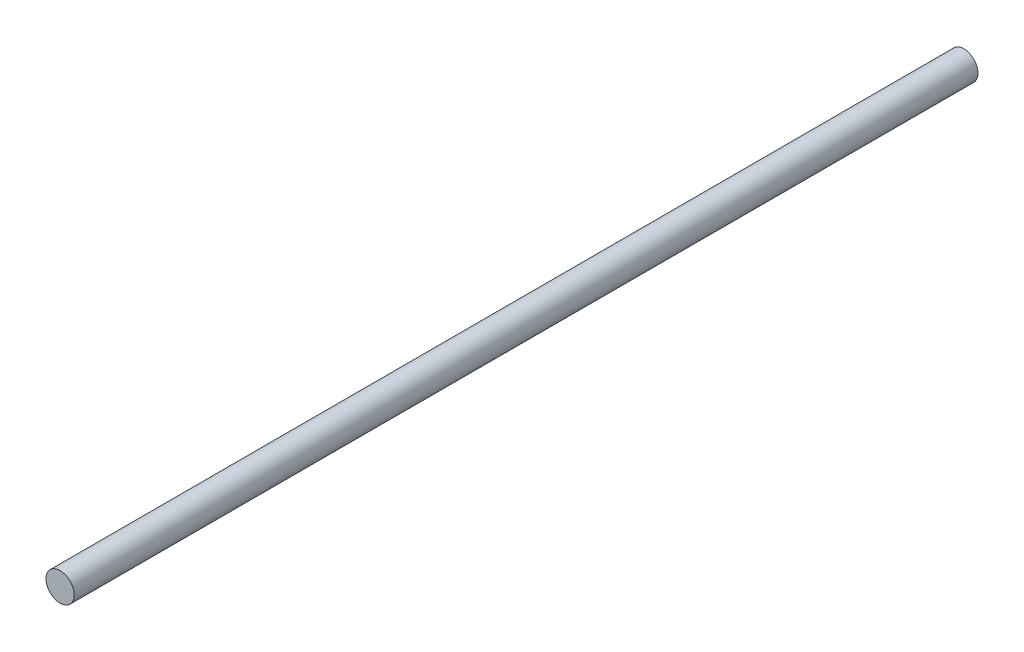
SolidWorks part; units mm, degrees
material "6061 Alloy"
ref_plane "Front Plane" through (0, 0, 0) normal (0, 0, 1) x (1, 0, 0)
ref_plane "Top Plane" through (0, 0, 0) normal (0, 1, 0) x (1, 0, 0)
ref_plane "Right Plane" through (0, 0, 0) normal (1, 0, 0) x (0, 0, -1)
sketch "Sketch1" plane through (0, 0, 0) normal (0, 0, 1) x (1, 0, 0)
  circle A0 centre (0, 0) radius 3.175
  dimension "D1" = 6.35
extrude "Boss-Extrude1" add sketch "Sketch1" along normal blind 203.2
